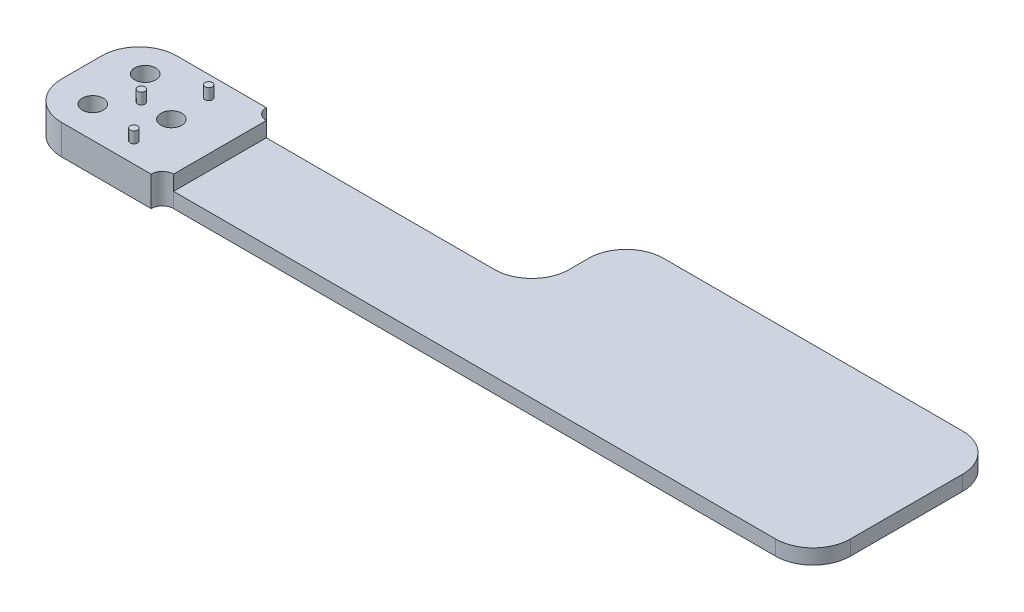
SolidWorks part; units mm, degrees
ref_plane "前视基准面" through (0, 0, 0) normal (0, 0, 1) x (1, 0, 0)
ref_plane "上视基准面" through (0, 0, 0) normal (0, 1, 0) x (1, 0, 0)
ref_plane "右视基准面" through (0, 0, 0) normal (1, 0, 0) x (0, 0, -1)
other "Configuration Table"
sketch "草图1" plane through (0, 0, 0) normal (0, 1, 0) x (1, 0, 0)
  line L1 (0, 0) -> (17, 0)
  line L2 (0, 0) -> (0, 12.4)
  line L3 (0, 12.4) -> (17, 12.4)
  line L4 (17, 0) -> (17, 12.4)
  line L5 (0, 0) -> (17, 12.4) construction
  line L6 (0, 12.4) -> (17, 0) construction
  point P4 (8.5, 6.2)
  dimension "D1" = 12.4
  dimension "D2" = 17
extrude "凸台-拉伸1" add sketch "草图1" along normal blind 4
sketch "草图2" plane through (0, 4, 0) normal (0, 1, 0) x (1, 0, 0)
  line L0 (0, 6.2) -> (17, 6.2) construction
  line L1 (0, 12.4) -> (0, 0) construction
  line L2 (17, 0) -> (17, 12.4) construction
  line L3 (5, 10.6119) -> (5, 1.8815) construction
  circle A0 centre (12, 6.2) radius 1.4
  circle A1 centre (5, 9.7) radius 1.4
  circle A2 centre (5, 2.7) radius 1.4
  point P14 (0, 0)
  point P15 (6.8105, 6.2)
  dimension "D1" = 2.8
  dimension "D2" = 5
  dimension "D3" = 7
  dimension "D4" = 7
extrude "切除-拉伸1" cut sketch "草图2" against normal blind 3
sketch "草图3" plane through (17, 0, 0) normal (1, 0, 0) x (0, 0, -1)
  line L0 (12.4, 4) -> (12.4, 0) construction
  line L1 (0, 0) -> (12.4, 0)
  line L2 (0, 0) -> (0, 2)
  line L3 (0, 2) -> (12.4, 2)
  line L4 (12.4, 0) -> (12.4, 2)
  line L5 (0, 0) -> (12.4, 2) construction
  line L6 (0, 2) -> (12.4, 0) construction
  point P4 (6.2, 1)
  dimension "D1" = 2
extrude "凸台-拉伸2" add sketch "草图3" along normal blind 37
sketch "草图4" plane through (0, 4, 0) normal (0, 1, 0) x (1, 0, 0)
  line L0 (0, 6.2) -> (35.3145, 6.2) construction
  line L1 (17, 12.4) -> (0, 12.4)
  line L2 (17, 12.4) -> (17, 13.9)
  line L3 (17, 13.9) -> (0, 13.9)
  line L4 (0, 12.4) -> (0, 13.9)
  line L5 (17, 12.4) -> (0, 13.9) construction
  line L6 (17, 13.9) -> (0, 12.4) construction
  line L7 (17, 0) -> (0, 0)
  line L8 (17, 0) -> (17, -1.5)
  line L9 (17, -1.5) -> (0, -1.5)
  line L10 (0, 0) -> (0, -1.5)
  line L11 (17, 0) -> (0, -1.5) construction
  line L12 (17, -1.5) -> (0, 0) construction
  line L13 (0, 12.4) -> (0, 0) construction
  point P4 (8.5, 13.15)
  point P10 (8.5, -0.75)
  dimension "D1" = 15.4
extrude "凸台-拉伸3" add sketch "草图4" against normal up to surface (4 mm away) up to face at (27, 0, -6.2)
fillet "圆角1" radius 5 2 edges at (0, 2, -13.9) (0, 2, 1.5)
sketch "草图5" plane through (0, 4, 0) normal (0, 1, 0) x (1, 0, 0)
  line L0 (12, 6.2) -> (12, 17.5448) construction
  line L1 (12, 6.2) -> (-1.399, 6.2) construction
  circle A0 centre (8, 6.2) radius 0.5
  circle A1 centre (12, 11.2) radius 0.5
  circle A2 centre (12, 1.2) radius 0.5
  dimension "D1" = 1
  dimension "D2" = 10
  dimension "D3" = 4
extrude "凸台-拉伸4" add sketch "草图5" along normal blind 1.5
sketch "草图6" plane through (0, 2, 0) normal (0, 1, 0) x (1, 0, 0)
  line L0 (17, -1.5) -> (17, 13.9) construction
  line L1 (54, 12.4) -> (17, 12.4) construction
  line L2 (17, 13.9) -> (17, 12.4)
  line L3 (17, 12.4) -> (18.5, 12.4)
  line L4 (54, 0) -> (17, 0) construction
  line L5 (17, -1.5) -> (17, 0)
  line L6 (17, 0) -> (18.5, 0)
  arc A0 (17, 13.9) -> (18.5, 12.4) centre (18.5, 13.9) ccw
  arc A1 (18.5, 0) -> (17, -1.5) centre (18.5, -1.5) ccw
  point P10 (0, 0)
  point P18 (0, 0)
extrude "凸台-拉伸5" add sketch "草图6" against normal up to surface (2 mm away) up to face at (18.3929, 0, -6.2)
sketch "草图7" plane through (0, 0, 0) normal (0, -1, 0) x (1, 0, 0)
  line L1 (54, 0) -> (104, 0)
  line L2 (54, 0) -> (54, -25)
  line L3 (54, -25) -> (104, -25)
  line L4 (104, 0) -> (104, -25)
  line L5 (54, 0) -> (104, -25) construction
  line L6 (54, -25) -> (104, 0) construction
  point P4 (79, -12.5)
  dimension "D1" = 50
  dimension "D2" = 25
extrude "凸台-拉伸6" add sketch "草图7" against normal up to surface (2 mm away) up to face at (29.7298, 2, -6.2)
fillet "圆角2" radius 5 2 edges at (54, 1, -25) (54, 1, -12.4)
fillet "圆角3" radius 5 2 edges at (104, 1, -25) (104, 1, 0)
sketch "草图8" plane through (0, 2, 0) normal (0, 1, 0) x (1, 0, 0)
  line L0 (99, 0) -> (18.5, 0) construction
  line L2 (18.5, 0) -> (18.5, 12.4)
  line L4 (17, 0) -> (17, 12.4)
  line L5 (18.5, 0) -> (17, 12.4) construction
  line L6 (18.5, 12.4) -> (17, 0) construction
  line L7 (17, -1.5) -> (17, 13.9) construction
  line L8 (17, 13.9) -> (17, -1.5)
  arc A5 (17, 13.9) -> (18.5, 12.4) centre (18.5, 13.9) ccw
  arc A6 (17, 13.9) -> (18.5, 12.4) centre (18.5, 13.9) ccw
  arc A8 (18.5, 0) -> (17, -1.5) centre (18.5, -1.5) ccw
  arc A9 (18.5, 0) -> (17, -1.5) centre (18.5, -1.5) ccw
  point P4 (17.75, 6.2)
  arc M14 (18.5, 12.4) -> (17, 13.9) centre (18.5, 13.9) cw
  line M15 (17, 13.9) -> (17, -1.5)
  arc M16 (17, -1.5) -> (18.5, 0) centre (18.5, -1.5) cw
  dimension "D1" = 1.5
  dimension "D2" = 0
  dimension "D3" = 0
extrude "凸台-拉伸7" add sketch "草图8" along normal up to surface (2 mm away) contours L2 M16 M14 M15 up to face at (12, 4, -1.7)
